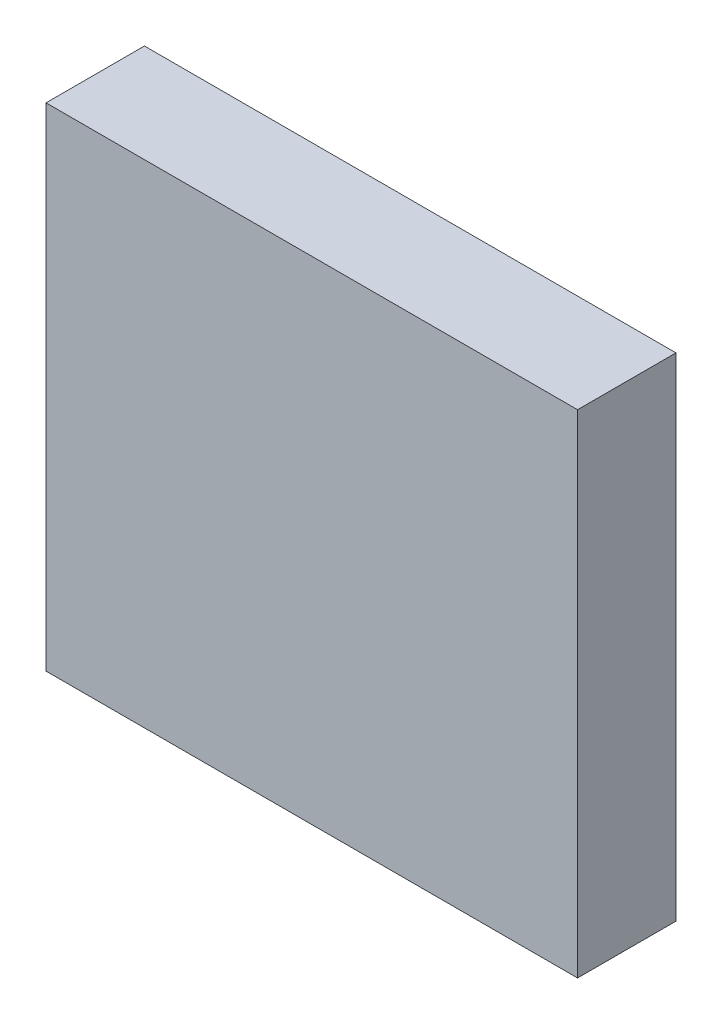
SolidWorks part; units mm, degrees
ref_plane "Plan de face" through (0, 0, 0) normal (0, 0, 1) x (1, 0, 0)
ref_plane "Plan de dessus" through (0, 0, 0) normal (0, 1, 0) x (1, 0, 0)
ref_plane "Plan de droite" through (0, 0, 0) normal (1, 0, 0) x (0, 0, -1)
sketch "Esquisse1" plane through (0, 0, 0) normal (0, 0, 1) x (1, 0, 0)
  line L1 (-135, 125) -> (135, 125)
  line L2 (-135, 125) -> (-135, -125)
  line L3 (-135, -125) -> (135, -125)
  line L4 (135, 125) -> (135, -125)
  line L5 (-135, 125) -> (135, -125) construction
  line L6 (-135, -125) -> (135, 125) construction
  point P0 (0, 0)
  dimension "D1" = 270
  dimension "D2" = 250
extrude "Boss.-Extru.1" add sketch "Esquisse1" along normal blind 50
